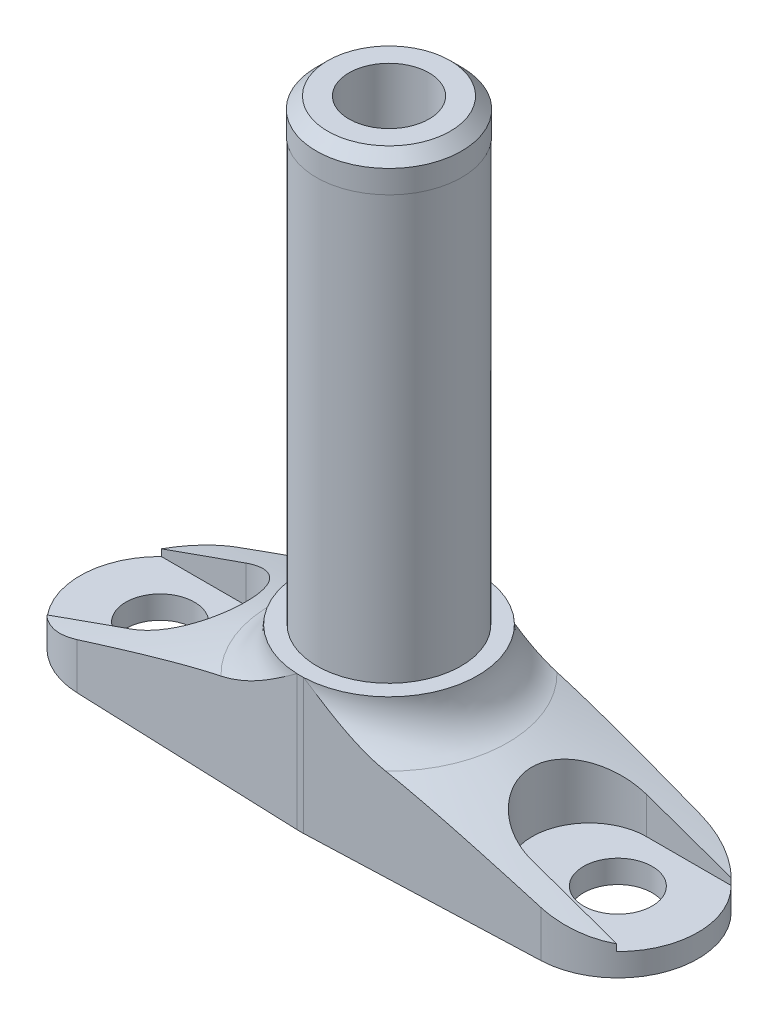
SolidWorks part; units mm, degrees
material "7075-T6 (SN)"
ref_plane "Płaszczyzna XY" through (0, 0, 0) normal (0, 0, 1) x (1, 0, 0)
ref_plane "Płaszczyzna XZ" through (0, 0, 0) normal (0, 1, 0) x (1, 0, 0)
ref_plane "Płaszczyzna YZ" through (0, 0, 0) normal (1, 0, 0) x (0, 0, -1)
sketch "Szkic1" plane through (0, 0, 0) normal (0, 0, 1) x (1, 0, 0)
  line L0 (0, 0) -> (0, 25) construction
  line L1 (0, 0) -> (0, 25)
  line L2 (0, 0) -> (27, 0)
  line L4 (0, 25) -> (27, 25)
  line L5 (27, 0) -> (27, 25)
  dimension "D1" = 54
  dimension "D2" = 25
revolve "Obrót1" add sketch "Szkic1" angle 360 about L0
sketch "Szkic2" plane through (0, 0, 0) normal (0, 0, 1) x (1, 0, 0)
  line L0 (0, 0) -> (0, 25) construction
  line L1 (27, 25) -> (-27, 25) construction
  line L2 (0, 25) -> (7.75, 25) construction
  line L3 (7.75, 25) -> (7.75, 9.0064)
  line L4 (7.75, 9.0064) -> (27, 2)
  line L5 (27, 0) -> (27, 25) construction
  line L6 (-27, 0) -> (27, 0) construction
  line L7 (7.75, 25) -> (27, 25)
  line L8 (27, 25) -> (27, 2)
  dimension "D1" = 2
  dimension "D2" = 20
  dimension "D3" = 15.5
revolve "Wycięcie-obrót1" cut sketch "Szkic2" angle 360 about L0
fillet "Zaokrąglenie1" radius 4 1 edges at (0, 9.0064, -7.75)
ref_plane "Płaszczyzna1" through (0, 2, 0) normal (0, 1, 0) x (1, 0, 0)
sketch "Szkic4" plane through (0, 2, 0) normal (0, 1, 0) x (1, 0, 0)
  line L0 (0, 8.8242) -> (0, -11.1289) construction
  circle A0 centre (-20, 0) radius 3
  circle A1 centre (20, 0) radius 3
  dimension "D1" = 6
  dimension "D2" = 6
  dimension "D3" = 40
extrude "Wytnij-wyciągnięcie3" cut sketch "Szkic4" against normal through all and the other way through all
sketch "Szkic3" plane through (0, 2, 0) normal (0, 1, 0) x (1, 0, 0)
  line L0 (-17.5, 5) -> (-26.533, 5)
  line L13 (-17.5, -5) -> (-26.533, -5)
  line L14 (17.5, 5) -> (26.533, 5)
  line L15 (17.5, -5) -> (26.533, -5)
  line L16 (0, 21.1527) -> (0, -20.0817) construction
  arc A1 (-17.5, -5) -> (-17.5, 5) centre (-17.5, 0) ccw
  arc A2 (17.5, 5) -> (17.5, -5) centre (17.5, 0) ccw
  circle A3 centre (0, 0) radius 27 construction
  arc A4 (-26.533, 5) -> (-26.533, -5) centre (0, 0) ccw
  arc A5 (26.533, -5) -> (26.533, 5) centre (0, 0) ccw
  dimension "D1" = 10
  dimension "D2" = 10
  dimension "D3" = 35
extrude "Wytnij-wyciągnięcie2" cut sketch "Szkic3" along normal through all
sketch "Szkic5" plane through (0, 0, 0) normal (0, -1, 0) x (1, 0, 0)
  line L0 (-20.2625, 6.9951) -> (-0.2906, 7.7445)
  line L1 (-20.2625, -6.9951) -> (-0.2906, -7.7445)
  line L2 (0.2906, 7.7445) -> (20.2625, 6.9951)
  line L3 (20.2625, -6.9951) -> (0.2906, -7.7445)
  arc A0 (-0.2906, -7.7445) -> (0.2906, -7.7445) centre (0, 0) ccw
  arc A1 (-20.2625, 6.9951) -> (-20.2625, -6.9951) centre (-20, 0) ccw
  arc A2 (20.2625, -6.9951) -> (20.2625, 6.9951) centre (20, 0) ccw
  circle A3 centre (0, 0) radius 27 construction
  arc A4 (0.2906, 7.7445) -> (-0.2906, 7.7445) centre (0, 0) ccw
  dimension "D1" = 15.5
extrude "Wytnij-wyciągnięcie4" cut sketch "Szkic5" against normal through all flip side to cut
sketch "Szkic8" plane through (0, 0, 0) normal (0, 0, 1) x (1, 0, 0)
  line L2 (0, 25) -> (0, 11.8073)
  line L5 (0, 11.8073) -> (7.75, 11.8073)
  line L6 (7.75, 11.8073) -> (7.75, 25) construction
  line L7 (7.75, 11.8073) -> (7.75, 25)
  line L8 (7.75, 25) -> (0, 25)
  line L9 (7.75, 11.8073) -> (0.2906, 11.8073) construction
  dimension "D1" = 0
revolve "Wycięcie-obrót2" cut sketch "Szkic8" angle 360 about L2
sketch "Szkic9" plane through (0, 0, 0) normal (0, 0, 1) x (1, 0, 0)
  line L2 (0, 11.8073) -> (0, 51.8073) construction
  line L3 (0, 51.8073) -> (5.35, 51.8073)
  line L5 (5.35, 51.8073) -> (6.35, 50.8073)
  line L6 (0, 51.8073) -> (6.35, 51.8073)
  line L7 (0, 51.8073) -> (0, 52.4234) construction
  line L8 (6.3, 48.8073) -> (6.35, 48.8073)
  line L9 (6.35, 50.8073) -> (6.35, 48.8073)
  line L10 (0, 11.8073) -> (0, 51.8073)
  line L11 (0.2906, 11.8073) -> (-0.2906, 11.8073) construction
  line L12 (6.3, 48.8073) -> (6.3, 11.8073)
  line L13 (6.3, 11.8073) -> (0, 11.8073)
  dimension "D1" = 0
  dimension "D2" = 40
  dimension "D3" = 12.7
  dimension "D4" = 3
  dimension "D5" = 6.3
revolve "Obrót2" add sketch "Szkic9" angle 360 about L2
sketch "Szkic10" plane through (0, 51.8073, 0) normal (0, 1, 0) x (1, 0, 0)
  circle A0 centre (0, 0) radius 3.5
  dimension "D1" = 7
extrude "Wytnij-wyciągnięcie5" cut sketch "Szkic10" against normal through all
equation "\"D3@Szkic3\"=40-2*1/2*5"
